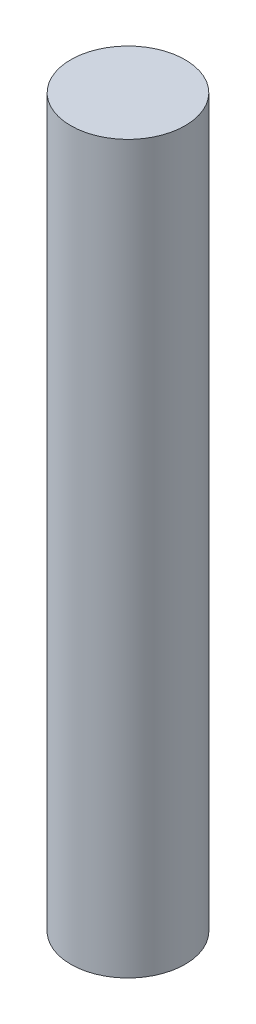
SolidWorks part; units mm, degrees
material "Alloy Steel"
ref_plane "Front Plane" through (0, 0, 0) normal (0, 0, 1) x (1, 0, 0)
ref_plane "Top Plane" through (0, 0, 0) normal (0, 1, 0) x (1, 0, 0)
ref_plane "Right Plane" through (0, 0, 0) normal (1, 0, 0) x (0, 0, -1)
other "Bounding Box"
ref_plane "Default Plane" through (-8.9266, -12.7485, 0) normal (-0.1736, 0.9848, 0) x (0.9848, 0.1736, 0)
sketch "Sketch1" plane through (0, 0, 0) normal (0, 1, 0) x (1, 0, 0)
  circle A0 centre (0, 0) radius 2.5
  dimension "D1" = 5
extrude "Boss-Extrude1" add sketch "Sketch1" along normal mid plane 31.75
